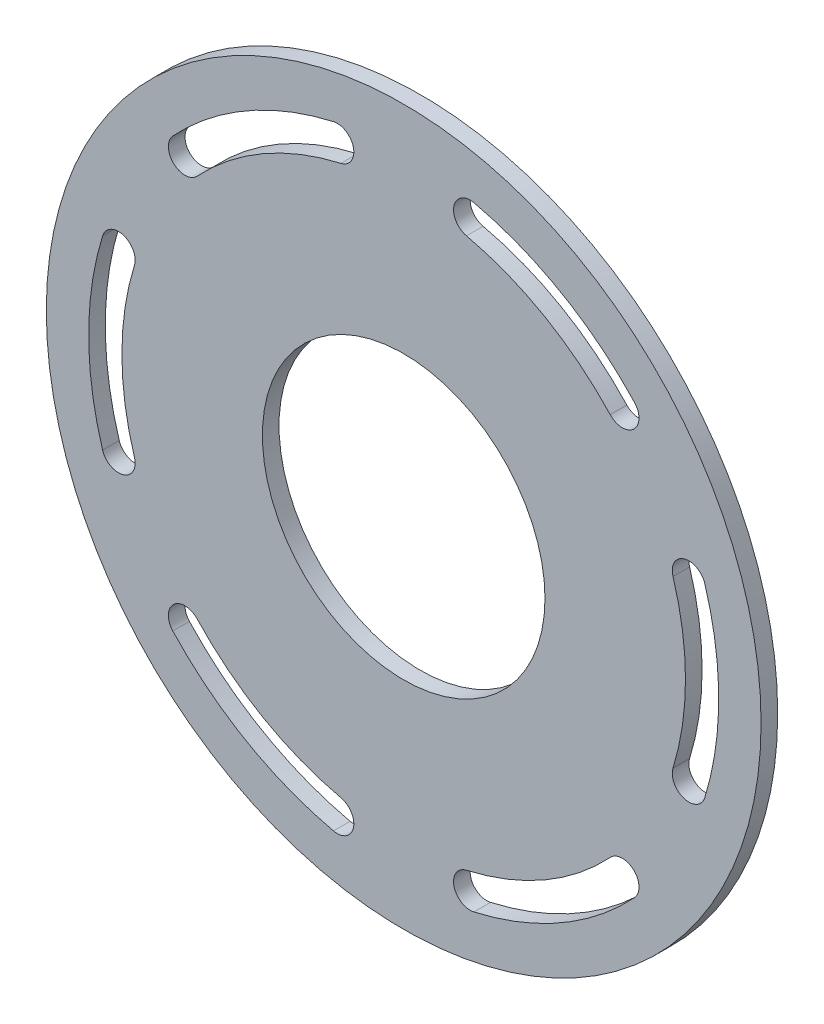
SolidWorks part; units mm, degrees
ref_plane "Front Plane" through (0, 0, 0) normal (0, 0, 1) x (1, 0, 0)
ref_plane "Top Plane" through (0, 0, 0) normal (0, 1, 0) x (1, 0, 0)
ref_plane "Right Plane" through (0, 0, 0) normal (1, 0, 0) x (0, 0, -1)
sketch "Sketch1" plane through (0, 0, 0) normal (0, 0, 1) x (1, 0, 0)
  line L0 (-28.4988, 49.3614) -> (0, 0) construction
  line L2 (0, -56.9976) -> (0, 56.9976) construction
  circle A0 centre (0, 0) radius 65.0875
  circle A1 centre (0, 0) radius 68.2625
  circle A2 centre (0, 0) radius 56.9976 construction
  arc A5 (-41.7704, 38.7809) -> (-12.7, 55.5647) centre (0, 0) cw construction
  arc A6 (-13.4074, 58.6599) -> (-44.0972, 40.9411) centre (0, 0) ccw
  arc A7 (-11.9926, 52.4695) -> (-39.4437, 36.6206) centre (0, 0) ccw
  arc A8 (-11.9926, 52.4695) -> (-13.4074, 58.6599) centre (-12.7, 55.5647) ccw
  arc A9 (-44.0972, 40.9411) -> (-39.4437, 36.6206) centre (-41.7704, 38.7809) ccw
  arc A14 (39.4437, 36.6206) -> (11.9926, 52.4695) centre (0, 0) ccw
  arc A19 (39.4437, 36.6206) -> (44.0972, 40.9411) centre (41.7704, 38.7809) ccw
  arc A24 (13.4074, 58.6599) -> (11.9926, 52.4695) centre (12.7, 55.5647) ccw
  arc A25 (44.0972, 40.9411) -> (13.4074, 58.6599) centre (0, 0) ccw
  arc A26 (12.7, 55.5647) -> (41.7704, 38.7809) centre (0, 0) cw construction
  arc A27 (51.4362, -15.8489) -> (51.4362, 15.8489) centre (0, 0) ccw
  arc A28 (51.4362, -15.8489) -> (57.5047, -17.7188) centre (54.4704, -16.7838) ccw
  arc A29 (57.5047, 17.7188) -> (51.4362, 15.8489) centre (54.4704, 16.7838) ccw
  arc A30 (57.5047, -17.7188) -> (57.5047, 17.7188) centre (0, 0) ccw
  arc A31 (54.4704, 16.7838) -> (54.4704, -16.7838) centre (0, 0) cw construction
  arc A32 (11.9926, -52.4695) -> (39.4437, -36.6206) centre (0, 0) ccw
  arc A33 (11.9926, -52.4695) -> (13.4074, -58.6599) centre (12.7, -55.5647) ccw
  arc A34 (44.0972, -40.9411) -> (39.4437, -36.6206) centre (41.7704, -38.7809) ccw
  arc A35 (13.4074, -58.6599) -> (44.0972, -40.9411) centre (0, 0) ccw
  arc A36 (41.7704, -38.7809) -> (12.7, -55.5647) centre (0, 0) cw construction
  arc A37 (-39.4437, -36.6206) -> (-11.9926, -52.4695) centre (0, 0) ccw
  arc A38 (-39.4437, -36.6206) -> (-44.0972, -40.9411) centre (-41.7704, -38.7809) ccw
  arc A39 (-13.4074, -58.6599) -> (-11.9926, -52.4695) centre (-12.7, -55.5647) ccw
  arc A40 (-44.0972, -40.9411) -> (-13.4074, -58.6599) centre (0, 0) ccw
  arc A41 (-12.7, -55.5647) -> (-41.7704, -38.7809) centre (0, 0) cw construction
  arc A42 (-51.4362, 15.8489) -> (-51.4362, -15.8489) centre (0, 0) ccw
  arc A43 (-51.4362, 15.8489) -> (-57.5047, 17.7188) centre (-54.4704, 16.7838) ccw
  arc A44 (-57.5047, -17.7188) -> (-51.4362, -15.8489) centre (-54.4704, -16.7838) ccw
  arc A45 (-57.5047, 17.7188) -> (-57.5047, -17.7188) centre (0, 0) ccw
  arc A46 (-54.4704, -16.7838) -> (-54.4704, 16.7838) centre (0, 0) cw construction
  circle A48 centre (0, 0) radius 26.9875
  point P8 (-28.4988, 49.3614)
  point P18 (0, 0)
  point P19 (-54.4704, 16.7838)
  point P22 (28.4988, 49.3614)
  point P29 (56.9976, 0)
  point P36 (28.4988, -49.3614)
  point P42 (0, 0)
  point P44 (-28.4988, -49.3614)
  point P51 (-56.9976, 0)
  point P56 (0, 0)
  point P57 (-41.7704, -38.7809)
  point P58 (11.9926, -55.5647)
  point P59 (54.4704, 16.7838)
  point P60 (54.4704, 16.7838)
  point P61 (0, 0)
  dimension "D1" = 130.175
  dimension "D3" = 113.9952
  dimension "D5" = 3.175
  dimension "D9" = 53.975
  dimension "D4" = 30
  dimension "D6" = 12.7
  dimension "D2" = 3.175
  dimension "D7" = 6
extrude "Boss-Extrude1" add sketch "Sketch1" along normal blind 3.175
